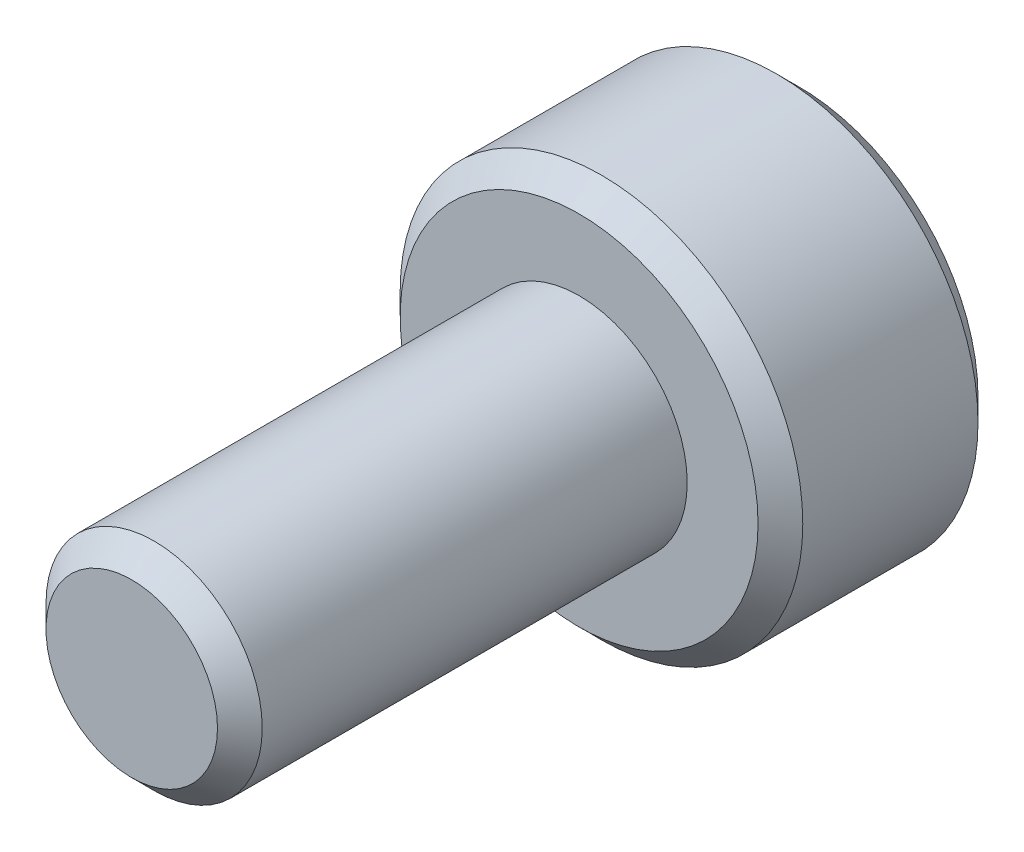
SolidWorks part; units mm, degrees
material "AISI 1020"
ref_plane "Front" through (0, 0, 0) normal (0, 0, 1) x (1, 0, 0)
ref_plane "Top" through (0, 0, 0) normal (0, 1, 0) x (1, 0, 0)
ref_plane "Right" through (0, 0, 0) normal (1, 0, 0) x (0, 0, -1)
sketch "Skizze1" plane through (0, 0, 0) normal (0, 0, 1) x (1, 0, 0)
  circle A0 centre (0, 0) radius 2.7
  dimension "D1" = 5.4
extrude "Aufsatz-Linear austragen1" add sketch "Skizze1" along normal blind 2.95
sketch "Skizze2" plane through (0, 0, 2.95) normal (0, 0, 1) x (1, 0, 0)
  circle A0 centre (0, 0) radius 1.45
  dimension "D1" = 2.9
extrude "Aufsatz-Linear austragen2" add sketch "Skizze2" along normal blind 6
chamfer "Fase1" distance 0.3 angle 45 3 edges at (2.7, 0, 2.95) (2.7, 0, 0) (1.45, 0, 8.95)
sketch "Skizze3" plane through (0, 0, 0) normal (0, 0, -1) x (-1, 0, 0)
  line L0 (1.25, 0) -> (0, 0) construction
  line L1 (1.25, 0.7217) -> (0, 1.4434)
  line L2 (0, 1.4434) -> (-1.25, 0.7217)
  line L3 (-1.25, 0.7217) -> (-1.25, -0.7217)
  line L4 (-1.25, -0.7217) -> (0, -1.4434)
  line L5 (0, -1.4434) -> (1.25, -0.7217)
  line L6 (1.25, -0.7217) -> (1.25, 0.7217)
  circle A0 centre (0, 0) radius 1.25 construction
  dimension "D1" = 2.5
extrude "Schnitt-Linear austragen1" cut sketch "Skizze3" against normal blind 2.5
